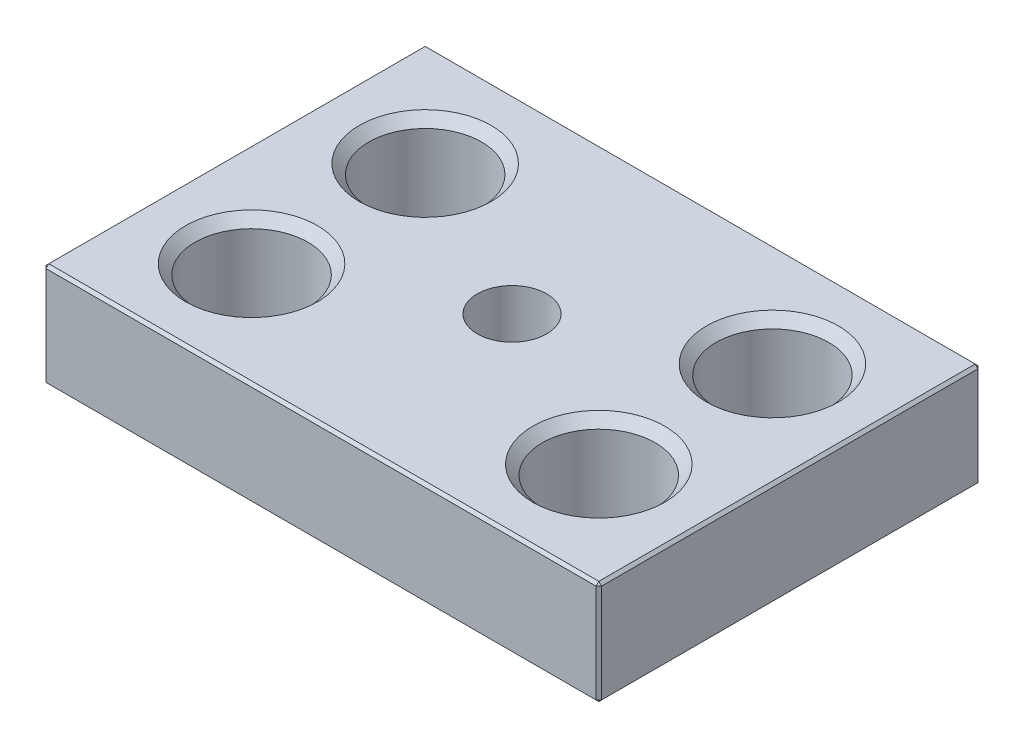
SolidWorks part; units mm, degrees
material "PTFE"
ref_plane "Front" through (0, 0, 0) normal (0, 0, 1) x (1, 0, 0)
ref_plane "Top" through (0, 0, 0) normal (0, 1, 0) x (1, 0, 0)
ref_plane "Right" through (0, 0, 0) normal (1, 0, 0) x (0, 0, -1)
sketch "Sketch1" plane through (0, 0, 0) normal (0, 1, 0) x (1, 0, 0)
  line L1 (-50.8, 34.925) -> (50.8, 34.925)
  line L2 (-50.8, 34.925) -> (-50.8, -34.925)
  line L3 (-50.8, -34.925) -> (50.8, -34.925)
  line L4 (50.8, 34.925) -> (50.8, -34.925)
  point P4 (0, 34.925)
  point P6 (50.8, 0)
  dimension "D1" = 101.6
  dimension "D2" = 69.85
extrude "Extrude1" add sketch "Sketch1" along normal blind 19.05
hole_wizard "13/16 (0.8125) Diameter Hole1" positions "Sketch4" profile "Sketch3" hole size "13/16" standard "Ansi Inch" end condition through all
sketch "Sketch4" plane through (0, 19.05, 0) normal (0, 1, 0) x (-1, 0, 0)
  line L1 (31.75, -15.875) -> (-31.75, -15.875) construction
  line L2 (31.75, -15.875) -> (31.75, 15.875) construction
  line L3 (31.75, 15.875) -> (-31.75, 15.875) construction
  line L4 (-31.75, -15.875) -> (-31.75, 15.875) construction
  point P0 (-31.75, 15.875)
  point P1 (-31.75, -15.875)
  point P3 (31.75, -15.875)
  point P5 (31.75, 15.875)
  point P123 (0, 15.875)
  point P125 (-31.75, 0)
  dimension "D1" = 63.5
  dimension "D2" = 31.75
sketch "Sketch3" plane through (31.75, 19.05, 15.875) normal (1, 0, 0) x (0, 0, 1)
  line L0 (0, 0) -> (0, 19.05)
  line L1 (0, 19.05) -> (12.065, 19.05)
  line L2 (10.3187, 17.3038) -> (10.3187, 1.7462)
  line L3 (10.3187, 1.7462) -> (12.065, 0)
  line L5 (12.065, 0) -> (0, 0)
  line L6 (-10.3187, 1.7462) -> (-12.065, 0) construction
  line L7 (12.065, 19.05) -> (10.3187, 17.3038)
  line L8 (-12.065, 19.05) -> (-10.3188, 17.3037) construction
  line L11 (0, -6.35) -> (0, 107.95) construction
  dimension "Thru Hole Dia." = 20.6375
  dimension "Thru Hole Depth" = 19.05
  dimension "Near C'Sink Dia." = 24.13
  dimension "Near C'Sink Angle" = 90
  dimension "Far C'Sink Dia." = 24.13
  dimension "Far C'Sink Angle" = 90
hole_wizard "CBORE for #10 Socket Head Cap Screw1" positions "Sketch6" profile "Sketch5" counterbore size "#10" standard "Ansi Inch" end condition through all
sketch "Sketch6" plane through (0, 19.05, 0) normal (0, 1, 0) x (-1, 0, 0)
  point P0 (0, 0)
sketch "Sketch5" plane through (0, 19.05, 0) normal (1, 0, 0) x (0, 0, 1)
  line L0 (0, 0) -> (0, 19.05)
  line L1 (0, 19.05) -> (2.8067, 19.05)
  line L3 (2.8067, 19.05) -> (2.8067, 15.24)
  line L4 (2.8067, 15.24) -> (6.35, 15.24)
  line L5 (6.35, 15.24) -> (6.35, 0)
  line L7 (6.35, 0) -> (0, 0)
  line L11 (0, -6.35) -> (0, 107.95) construction
  dimension "Thru Hole Dia." = 5.6134
  dimension "Thru Hole Depth" = 19.05
  dimension "C'Bore Dia." = 12.7
  dimension "C'Bore Depth" = 15.24
chamfer "Chamfer1" distance 0.508 angle 45 12 edges at (-50.8, 9.525, 34.925) (0, 0, 34.925) (-50.8, 0, 0) (-50.8, 9.525, -34.925) (-50.8, 19.05, 0) (0, 19.05, 34.925) (50.8, 9.525, 34.925) (0, 19.05, -34.925) (50.8, 19.05, 0) (50.8, 9.525, -34.925) (50.8, 0, 0) (0, 0, -34.925)
